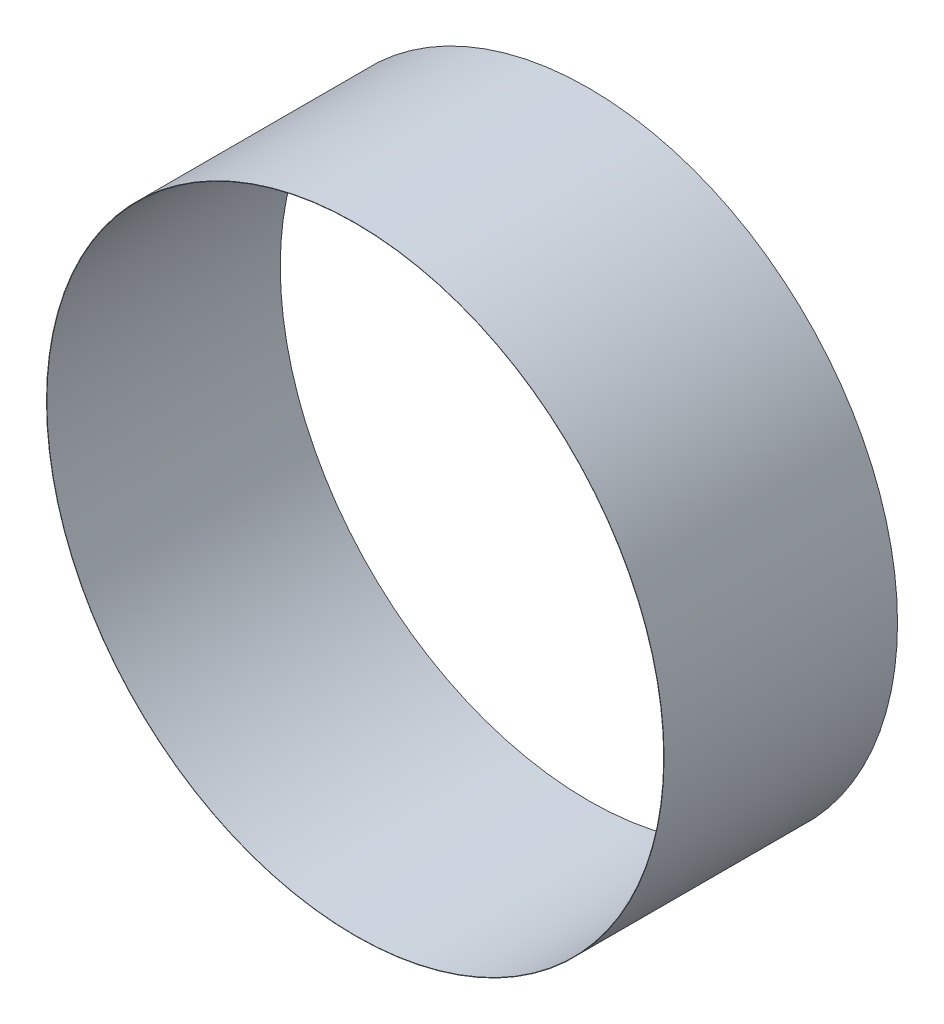
SolidWorks part; units mm, degrees
ref_plane "前视基准面" through (0, 0, 0) normal (0, 0, 1) x (1, 0, 0)
ref_plane "上视基准面" through (0, 0, 0) normal (0, 1, 0) x (1, 0, 0)
ref_plane "右视基准面" through (0, 0, 0) normal (1, 0, 0) x (0, 0, -1)
sketch "草图1" plane through (0, 0, 0) normal (0, 0, 1) x (1, 0, 0)
  circle A0 centre (0, 0) radius 92.5
  circle A2 centre (0, 0) radius 92.6
  dimension "D1" = 185
  dimension "D2" = 0.1
extrude "凸台-拉伸1" add sketch "草图1" along normal blind 70
